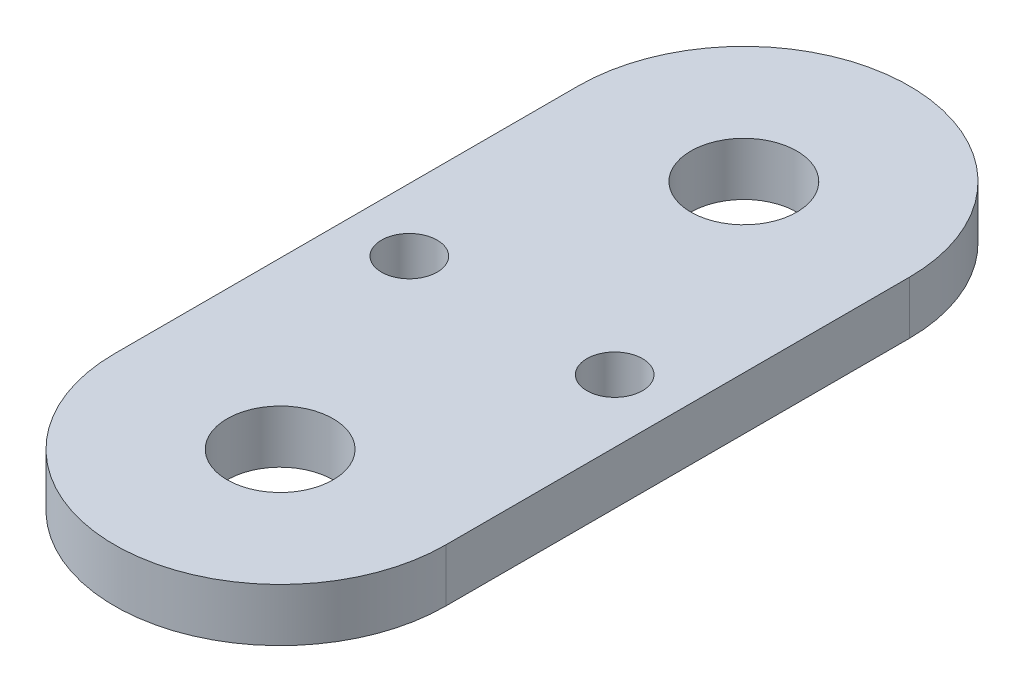
SolidWorks part; units mm, degrees
ref_plane "Front Plane" through (0, 0, 0) normal (0, 0, 1) x (1, 0, 0)
ref_plane "Top Plane" through (0, 0, 0) normal (0, 1, 0) x (1, 0, 0)
ref_plane "Right Plane" through (0, 0, 0) normal (1, 0, 0) x (0, 0, -1)
sketch "Sketch1" plane through (0, 0, 0) normal (0, 1, 0) x (1, 0, 0)
  line L0 (-7.75, 0) -> (7.75, 0) construction
  line L1 (0, 17.5) -> (0, -17.5) construction
  line L2 (12.5, -30) -> (-12.5, -30)
  line L3 (12.5, -30) -> (12.5, 30)
  line L4 (12.5, 30) -> (-12.5, 30)
  line L5 (-12.5, -30) -> (-12.5, 30)
  line L6 (12.5, -30) -> (-12.5, 30) construction
  line L7 (12.5, 30) -> (-12.5, -30) construction
  circle A0 centre (-7.75, 0) radius 2.1
  circle A1 centre (7.75, 0) radius 2.1
  circle A2 centre (0, -17.5) radius 4
  circle A3 centre (0, 17.5) radius 4
  circle A4 centre (0, 17.5) radius 12.5
  circle A5 centre (0, -17.5) radius 12.5
  point P4 (0, 0)
  dimension "D2" = 4.2
  dimension "D5" = 8
  dimension "D1" = 15.5
  dimension "D3" = 25
  dimension "D4" = 35
extrude "Boss-Extrude1" add sketch "Sketch1" along normal blind 4 contours A4 A3 | A5 L3 A4 L5 A1 A0 | A5 A2
equation "\"m3 hole\"= 3.2"
equation "\"m4 hole\"= 4.2"
equation "\"m5 hole\"= 5.2"
equation "\"m6 hole\"= 6.2"
equation "\"m8 hole\"= 8.2"
equation "\"m3 tapped\"= 2.5"
equation "\"m4 tapped\"= 3.3"
equation "\"m5 tapped\"= 4.2"
equation "\"m6 tapped\"= 5"
equation "\"m8 tapped\"= 6.8"
